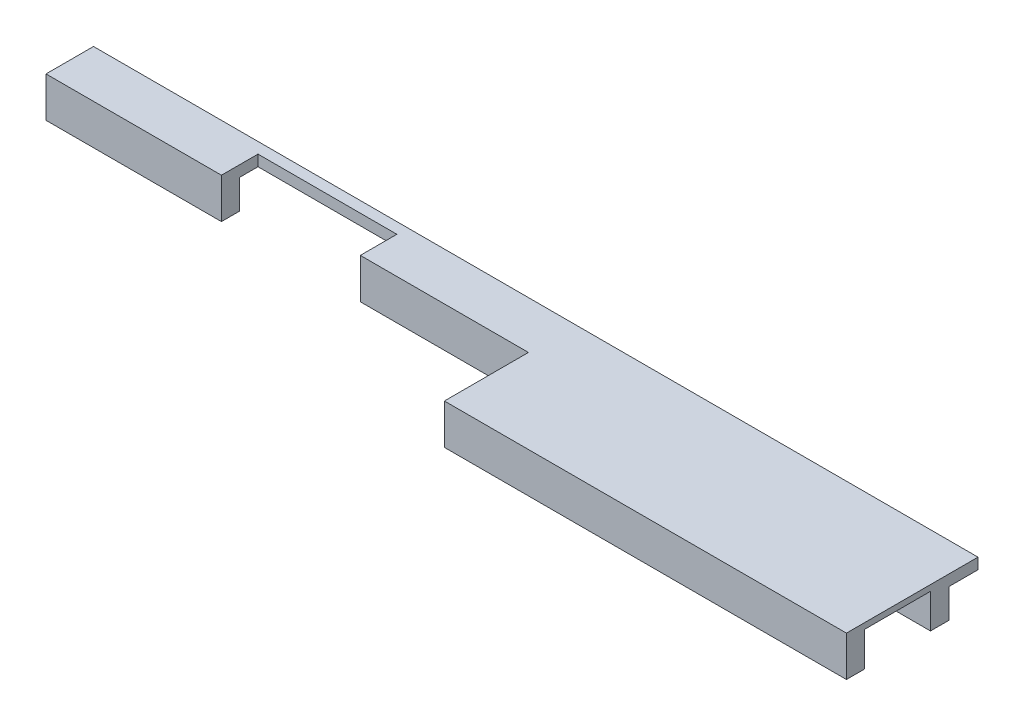
SolidWorks part; units mm, degrees
ref_plane "Front Plane" through (0, 0, 0) normal (0, 0, 1) x (1, 0, 0)
ref_plane "Top Plane" through (0, 0, 0) normal (0, 1, 0) x (1, 0, 0)
ref_plane "Right Plane" through (0, 0, 0) normal (1, 0, 0) x (0, 0, -1)
sketch "Sketch1" plane through (0, 0, 0) normal (0, 1, 0) x (1, 0, 0)
  line L1 (-60, -68.5) -> (60, -68.5)
  line L2 (-60, -68.5) -> (-60, 68.5)
  line L3 (-60, 68.5) -> (60, 68.5)
  line L4 (60, -68.5) -> (60, 68.5)
  line L5 (-60, -68.5) -> (60, 68.5) construction
  line L6 (-60, 68.5) -> (60, -68.5) construction
  point P0 (0, 0)
  dimension "D1" = 137
  dimension "D2" = 120
extrude "Boss-Extrude1" add sketch "Sketch1" along normal blind 3
sketch "Sketch2" plane through (0, 3, 0) normal (0, 1, 0) x (1, 0, 0)
  line L0 (60, -68.5) -> (60, 68.5) construction
  line L1 (-60, -68.5) -> (60, -68.5)
  line L2 (-60, -68.5) -> (-60, -63.5)
  line L3 (-60, -63.5) -> (60, -63.5)
  line L4 (60, -68.5) -> (60, -63.5)
  dimension "D1" = 5
extrude "Boss-Extrude2" add sketch "Sketch2" along normal blind 8
sketch "Sketch3" plane through (0, 11, 0) normal (0, 1, 0) x (1, 0, 0)
  line L1 (-19, -58.5) -> (19, -58.5)
  line L2 (-19, -58.5) -> (-19, -68.5)
  line L3 (-19, -68.5) -> (19, -68.5)
  line L4 (19, -58.5) -> (19, -68.5)
  line L5 (-60, -68.5) -> (60, -68.5) construction
  line L6 (0, 0) -> (0, -68.5) construction
  dimension "D1" = 38
  dimension "D3" = 10
extrude "Cut-Extrude1" cut sketch "Sketch3" against normal blind 25
sketch "Sketch4" plane through (0, 3, 0) normal (0, 1, 0) x (1, 0, 0)
  line L1 (-60, 68.5) -> (60, 68.5)
  line L2 (-60, 68.5) -> (-60, -55.5)
  line L3 (-60, -55.5) -> (60, -55.5)
  line L4 (60, 68.5) -> (60, -55.5)
  line L5 (-60, -68.5) -> (-19, -68.5) construction
  line L6 (60, -63.5) -> (60, 68.5) construction
  dimension "D1" = 13
extrude "Cut-Extrude2" cut sketch "Sketch4" against normal through all both and the other way through all
sketch "Sketch7" plane through (-60, 0, 0) normal (-1, 0, 0) x (0, 0, 1)
  line L0 (63.5, 11) -> (63.5, 3)
  line L1 (63.5, 3) -> (55.5, 3)
  line L2 (63.5, 11) -> (68.5, 11)
  line L3 (68.5, 11) -> (68.5, 0)
  line L4 (68.5, 0) -> (55.5, 0)
  line L5 (55.5, 0) -> (55.5, 3)
extrude "Boss-Extrude3" add sketch "Sketch7" along normal blind 7
sketch "Sketch8" plane through (60, 0, 0) normal (1, 0, 0) x (0, 0, -1)
  line L0 (-55.5, 0) -> (-55.5, 3)
  line L1 (-55.5, 3) -> (-63.5, 3)
  line L2 (-63.5, 3) -> (-63.5, 11)
  line L3 (-63.5, 11) -> (-68.5, 11)
  line L4 (-68.5, 11) -> (-68.5, 1.6)
  line L5 (-68.5, 11) -> (-68.5, 0) construction
  line L6 (-68.5, 1.6) -> (-86.5, 1.6)
  line L7 (-86.5, 1.6) -> (-86.5, 11)
  line L8 (-86.5, 11) -> (-91.5, 11)
  line L9 (-91.5, 11) -> (-91.5, 0)
  line L10 (-91.5, 0) -> (-55.5, 0)
  dimension "D1" = 5
  dimension "D2" = 18
  dimension "D3" = 1.4
extrude "Boss-Extrude4" add sketch "Sketch8" along normal blind 120
mirror "Mirror2" about plane through (0, 0, 0) normal (0, -1, 0) of bodies 109
delete or keep bodies "Body-Delete/Keep 1" type delete bodies bodies 109
sketch "Sketch9" plane through (0, -11, 0) normal (0, -1, 0) x (-1, 0, 0)
  line L0 (-180, -68.5) -> (-60, -68.5) construction
  line L1 (-60, -91.5) -> (-65, -91.5)
  line L2 (-60, -91.5) -> (-60, -68.5)
  line L3 (-60, -68.5) -> (-65, -68.5)
  line L4 (-65, -91.5) -> (-65, -68.5)
  dimension "D1" = 5
extrude "Cut-Extrude3" cut sketch "Sketch9" against normal through all both and the other way through all
other "Move Face1" face at (180, -5.32, 73.1) parameters "D1"=5
